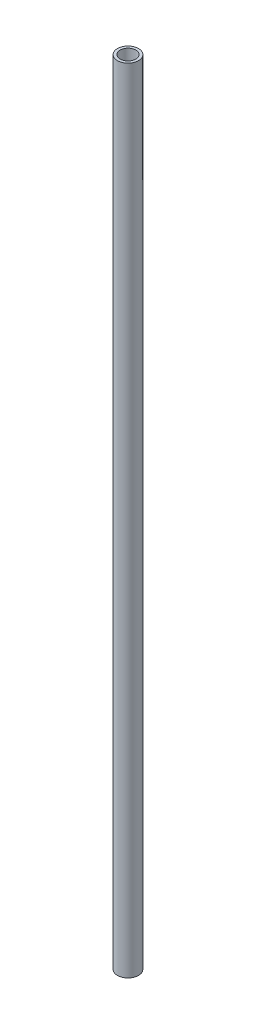
SolidWorks part; units mm, degrees
material "Copper"
ref_plane "Front Plane" through (0, 0, 0) normal (0, 0, 1) x (1, 0, 0)
ref_plane "Top Plane" through (0, 0, 0) normal (0, 1, 0) x (1, 0, 0)
ref_plane "Right Plane" through (0, 0, 0) normal (1, 0, 0) x (0, 0, -1)
sketch "Sketch1" plane through (0, 0, 0) normal (0, 1, 0) x (1, 0, 0)
  circle A0 centre (0, 0) radius 2
  circle A1 centre (0, 0) radius 1.5
  dimension "D1" = 4
  dimension "D2" = 3
extrude "Boss-Extrude1" add sketch "Sketch1" along normal mid plane 151
